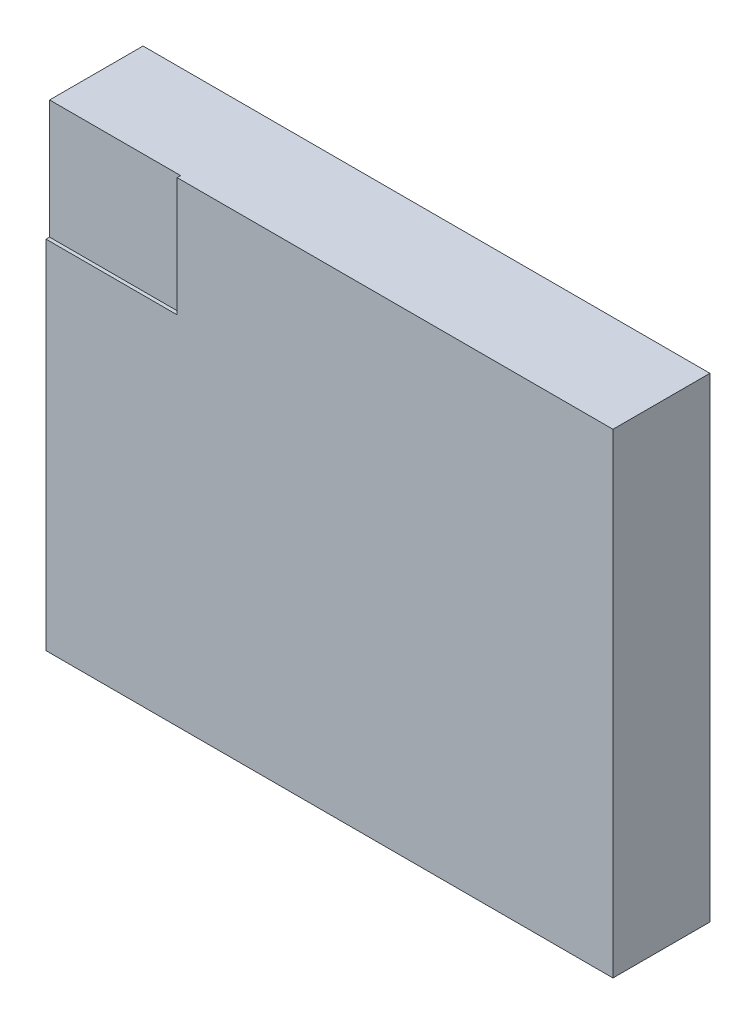
SolidWorks part; units mm, degrees
ref_plane "Front Plane" through (0, 0, 0) normal (0, 0, 1) x (1, 0, 0)
ref_plane "Top Plane" through (0, 0, 0) normal (0, 1, 0) x (1, 0, 0)
ref_plane "Right Plane" through (0, 0, 0) normal (1, 0, 0) x (0, 0, -1)
sketch "Sketch1" plane through (0, 0, 0) normal (0, 0, 1) x (1, 0, 0)
  line L1 (-0.804, -0.674) -> (0.804, -0.674)
  line L2 (-0.804, -0.674) -> (-0.804, 0.674)
  line L3 (-0.804, 0.674) -> (0.804, 0.674)
  line L4 (0.804, -0.674) -> (0.804, 0.674)
  line L5 (-0.804, -0.674) -> (0.804, 0.674) construction
  line L6 (-0.804, 0.674) -> (0.804, -0.674) construction
  point P0 (0, 0)
  dimension "D1" = 1.348
  dimension "D2" = 1.608
extrude "Boss-Extrude1" add sketch "Sketch1" along normal blind 0.275 from offset 0.164 contours L4 L3 L2 L1
sketch "Sketch2" plane through (0, 0, 0.439) normal (0, 0, 1) x (1, 0, 0)
  line L1 (-0.804, 0.674) -> (-0.4322, 0.674)
  line L2 (-0.804, 0.674) -> (-0.804, 0.337)
  line L3 (-0.804, 0.337) -> (-0.4322, 0.337)
  line L4 (-0.4322, 0.674) -> (-0.4322, 0.337)
extrude "Cut-Extrude1" cut sketch "Sketch2" against normal blind 0.01
sketch "Sketch3" plane through (0, 0, 0) normal (0, 1, 0) x (1, 0, 0)
  line L0 (-0.35, -0.164) -> (-0.35, 0) construction
  line L1 (-0.804, -0.164) -> (0.804, -0.164) construction
  line L2 (-0.35, 0) -> (0, 0) construction
  line L3 (-0.35, 0) -> (-0.35, -0.164)
  line L4 (-0.35, -0.164) -> (-0.2594, -0.164)
  arc A0 (-0.2594, -0.164) -> (-0.35, 0) centre (-0.35, -0.107) ccw
  dimension "D2" = 0.214
  dimension "D1" = 0.35
revolve "Revolve5" add sketch "Sketch3" angle 360 about L3
pattern_linear "LPattern1" count 2 spacing 0.4 along (0, 1, 0) count 2 spacing 0.4 along (0, -1, 0) of "Revolve5"
sketch "Sketch5" plane through (0, 0, 0.164) normal (0, 0, -1) x (-1, 0, 0)
  line L0 (0, 0) -> (0, 0.2) construction
  line L1 (0, 0) -> (0, -0.2)
  point P5 (0, 0.2)
  point P6 (0, -0.2)
  dimension "D1" = 0.2
  dimension "D2" = 0.2
pattern_sketch "Sketch-Pattern1" of "Revolve5" driven by "Sketch5"
mirror "Mirror1" about plane through (0, 0, 0) normal (1, 0, 0) of "LPattern1", "Revolve5"
